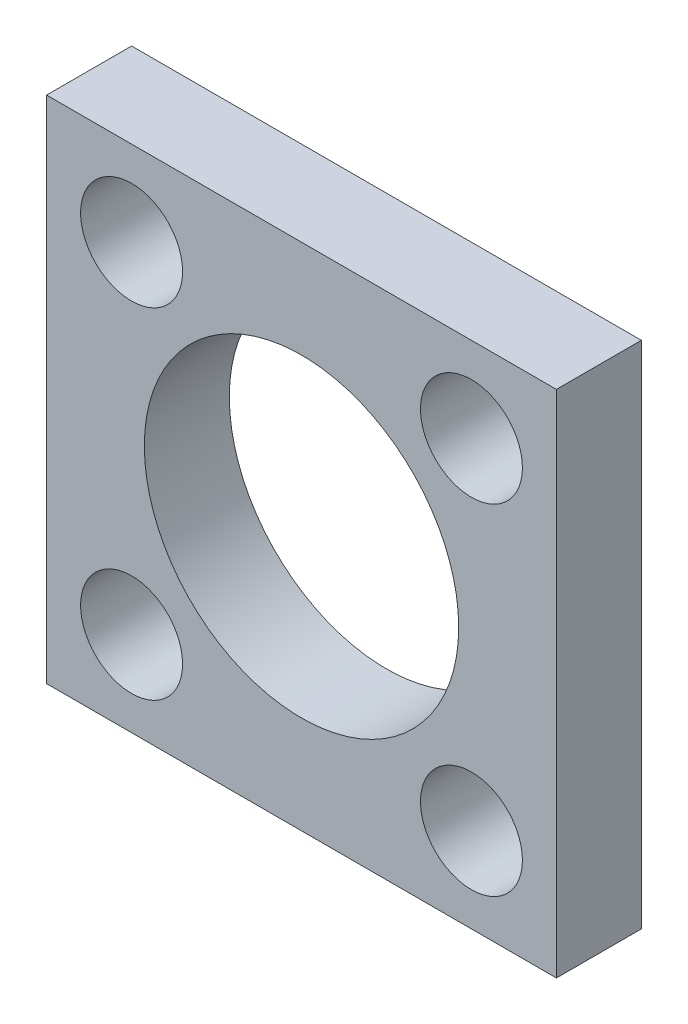
SolidWorks part; units mm, degrees
ref_plane "Ön Düzlem" through (0, 0, 0) normal (0, 0, 1) x (1, 0, 0)
ref_plane "Üst Düzlem" through (0, 0, 0) normal (0, 1, 0) x (1, 0, 0)
ref_plane "Sağ Düzlem" through (0, 0, 0) normal (1, 0, 0) x (0, 0, -1)
sketch "Çizim1" plane through (0, 0, 0) normal (0, 0, 1) x (1, 0, 0)
  line L0 (-20, -20) -> (20, -20) construction
  line L1 (-20, -20) -> (-20, 20) construction
  line L2 (-20, 20) -> (20, 20) construction
  line L3 (20, -20) -> (20, 20) construction
  line L4 (-20, -20) -> (20, 20) construction
  line L5 (-20, 20) -> (20, -20) construction
  line L6 (-30, -30) -> (30, -30)
  line L7 (-30, -30) -> (-30, 30)
  line L8 (-30, 30) -> (30, 30)
  line L9 (30, -30) -> (30, 30)
  line L10 (-30, -30) -> (30, 30) construction
  line L11 (-30, 30) -> (30, -30) construction
  circle A0 centre (0, 0) radius 18.5
  circle A1 centre (20, 20) radius 6
  circle A2 centre (-20, 20) radius 6
  circle A3 centre (20, -20) radius 6
  circle A4 centre (-20, -20) radius 6
  dimension "D1" = 37
  dimension "D3" = 12
  dimension "D2" = 40
  dimension "D4" = 60
extrude "Yükseklik-Ekstrüzyon1" add sketch "Çizim1" along normal blind 10
